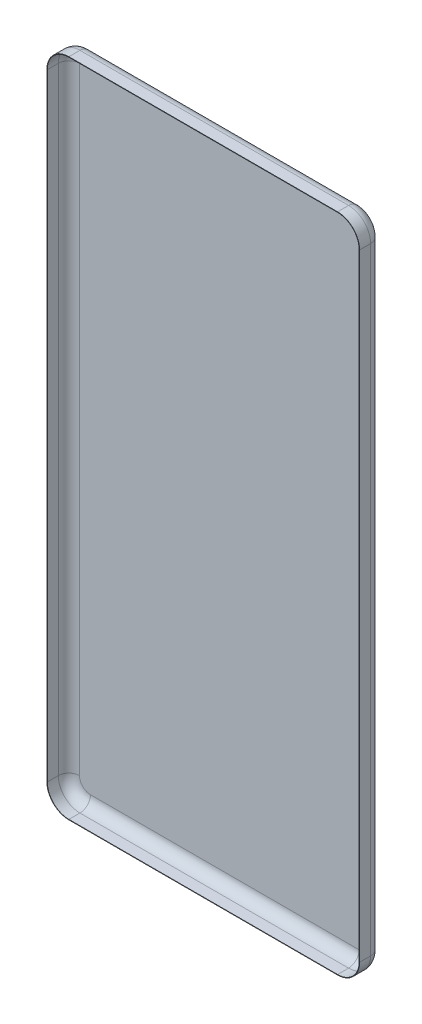
SolidWorks part; units mm, degrees
material "Natural Rubber"
ref_plane "Front Plane" through (0, 0, 0) normal (0, 0, 1) x (1, 0, 0)
ref_plane "Top Plane" through (0, 0, 0) normal (0, 1, 0) x (1, 0, 0)
ref_plane "Right Plane" through (0, 0, 0) normal (1, 0, 0) x (0, 0, -1)
sketch "Sketch1" plane through (0, 0, 0) normal (0, 0, 1) x (1, 0, 0)
  line L1 (-1300, 0) -> (-81, 0)
  line L2 (-1400, -100) -> (-1400, -2899)
  line L3 (-1300, -2999) -> (-81, -2999)
  line L4 (19, -100) -> (19, -2899)
  arc A0 (-1400, -2899) -> (-1300, -2999) centre (-1300, -2899) ccw
  arc A1 (-81, -2999) -> (19, -2899) centre (-81, -2899) ccw
  arc A2 (-81, 0) -> (19, -100) centre (-81, -100) cw
  arc A3 (-1300, 0) -> (-1400, -100) centre (-1300, -100) ccw
  point P6 (-1400, -2999)
  point P11 (19, 0)
  point P14 (-1400, 0)
  dimension "D3" = 100
  dimension "D1" = 1419
  dimension "D2" = 2999
extrude "Boss-Extrude1" add sketch "Sketch1" along normal blind 200
fillet "Fillet1" radius 50 16 edges at (-1370.7107, -2969.7107, 0) (-690.5, -2999, 0) (-10.2893, -2969.7107, 0) (19, -1499.5, 0) (-10.2893, -29.2893, 0) (-690.5, 0, 0) (-1370.7107, -29.2893, 0) (-1400, -1499.5, 0) (-1370.7107, -2969.7107, 200) (-690.5, -2999, 200) (-10.2893, -2969.7107, 200) (19, -1499.5, 200) (-10.2893, -29.2893, 200) (-690.5, 0, 200) (-1370.7107, -29.2893, 200) (-1400, -1499.5, 200)
sketch "Sketch2" plane through (19, 0, 0) normal (1, 0, 0) x (0, 0, -1)
  line L0 (-150, 0) -> (-50, 0) construction
  line L1 (-100, 0) -> (-278.4133, 0)
  line L2 (-100, 0) -> (-100, -3000)
  line L3 (-100, -3000) -> (-278.4133, -3000)
  line L4 (-278.4133, 0) -> (-278.4133, -3000)
  point P6 (0, 0)
  dimension "D1" = 3000
extrude "Cut-Extrude1" cut sketch "Sketch2" against normal through all
shell "Shell1" thickness 2
